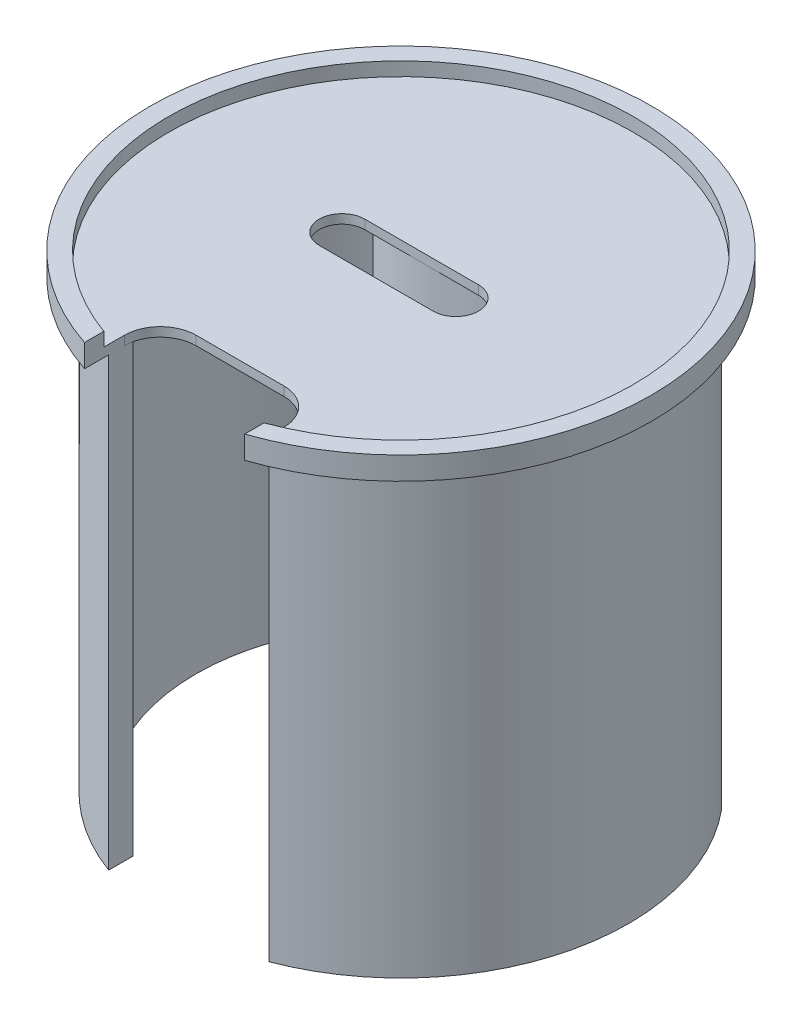
SolidWorks part; units mm, degrees
ref_plane "Front Plane" through (0, 0, 0) normal (0, 0, 1) x (1, 0, 0)
ref_plane "Top Plane" through (0, 0, 0) normal (0, 1, 0) x (1, 0, 0)
ref_plane "Right Plane" through (0, 0, 0) normal (1, 0, 0) x (0, 0, -1)
sketch "Sketch3" plane through (0, 0, 0) normal (0, 1, 0) x (1, 0, 0)
  line L0 (-16.4485, 0) -> (15.3015, 0) construction
  line L1 (-16.4485, 6.35) -> (15.3015, 6.35)
  line L2 (-16.4485, -6.35) -> (15.3015, -6.35)
  circle A0 centre (0, 0) radius 69.85
  arc A2 (-16.4485, 6.35) -> (-16.4485, -6.35) centre (-16.4485, 0) ccw
  arc A3 (15.3015, -6.35) -> (15.3015, 6.35) centre (15.3015, 0) ccw
  point P5 (-0.5735, 0)
extrude "Boss-Extrude1" add sketch "Sketch3" along normal blind 6.35
sketch "Sketch4" plane through (0, 6.35, 0) normal (0, 1, 0) x (1, 0, 0)
  circle A0 centre (0, 0) radius 64.77
extrude "Cut-Extrude1" cut sketch "Sketch4" against normal blind 3.81
sketch "Sketch5" plane through (0, 6.35, 0) normal (0, 1, 0) x (1, 0, 0)
  line L1 (22.5372, -45.2053) -> (-21.9128, -45.2053)
  line L2 (22.5372, -45.2053) -> (22.5372, -70.6053)
  line L3 (22.5372, -70.6053) -> (-21.9128, -70.6053)
  line L4 (-21.9128, -45.2053) -> (-21.9128, -70.6053)
  dimension "D1" = 25.4
  dimension "D2" = 44.45
extrude "Cut-Extrude2" cut sketch "Sketch5" against normal through all
fillet "Fillet1" radius 10 2 edges at (22.5372, 1.27, 45.2053) (-21.9128, 1.27, 45.2053)
sketch "Sketch8" plane through (0, 0, 0) normal (0, -1, 0) x (1, 0, 0)
  line L0 (34.2582, -40.64) -> (30.4482, -40.64)
  line L1 (-30.4482, -40.64) -> (-34.2582, -40.64)
  arc A3 (34.2582, -40.64) -> (-34.2582, -40.64) centre (0, -40.64) ccw
  arc A4 (30.4482, -40.64) -> (-30.4482, -40.64) centre (0, -40.64) ccw
  point P0 (0, -40.64)
  dimension "D2" = 3.81
  dimension "D1" = 40.64
extrude "Boss-Extrude2" add sketch "Sketch8" along normal blind 82.55
sketch "Sketch11" plane through (0, 2.54, 0) normal (0, 1, 0) x (1, 0, 0)
  line L0 (-40.181, 40.64) -> (-48.7918, 40.64)
  line L1 (-48.7918, 40.64) -> (-40.181, 40.64)
  line L2 (40.181, 40.64) -> (48.7918, 40.64)
  line L3 (-21.9128, -59.5993) -> (-21.9128, -52.7821)
  line L4 (-21.9128, -55.2053) -> (-21.9128, -66.3238) construction
  line L5 (22.5372, -59.366) -> (22.5372, -52.5186)
  line L6 (22.5372, -66.1143) -> (22.5372, -55.2053) construction
  arc A1 (-40.181, 40.64) -> (-21.9128, -52.7821) centre (0, 0) ccw
  arc A3 (22.5372, -52.5186) -> (40.181, 40.64) centre (0, 0) ccw
  arc A4 (-48.7918, 40.64) -> (-21.5904, -59.7169) centre (0, 0) ccw
  arc A5 (22.5372, -59.366) -> (48.7918, 40.64) centre (0, 0) ccw
  line M1 (22.5372, -55.2053) -> (22.5372, -60.7226)
  line M3 (-21.9128, -60.9506) -> (-21.9128, -55.2053)
extrude "Boss-Extrude3" add sketch "Sketch11" against normal blind 127 contours L0 A4 L3 A1 M3 | A5 L2 A3 L5 M1
